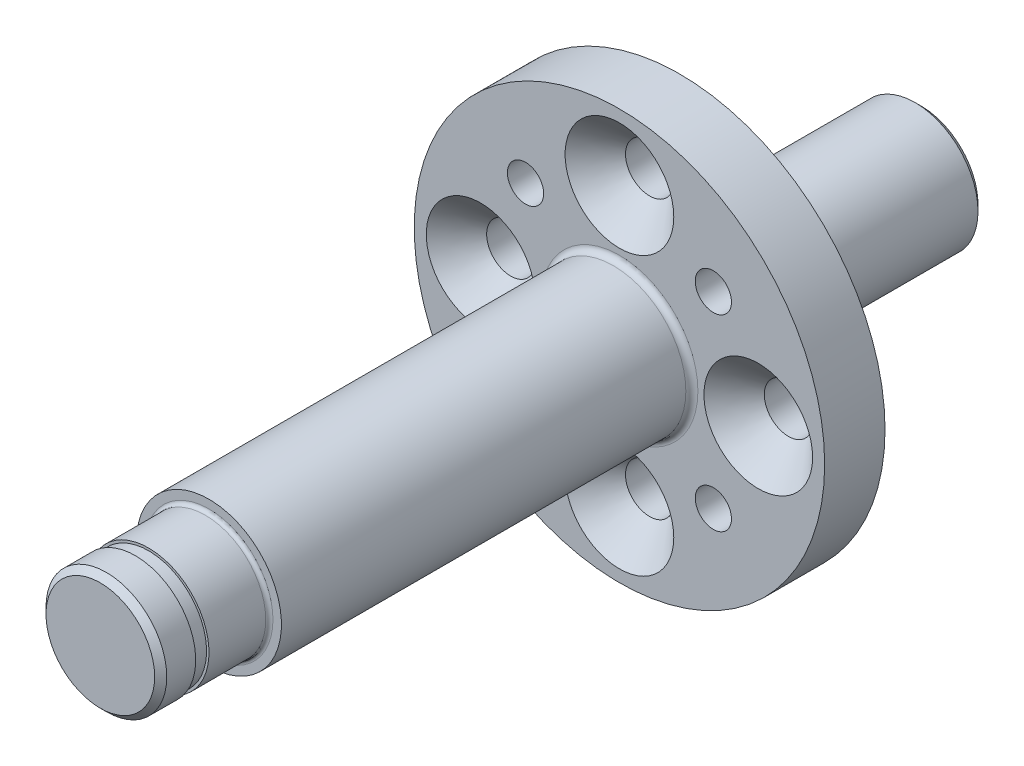
SolidWorks part; units mm, degrees
material "6063-T6"
ref_plane "Front Plane" through (0, 0, 0) normal (0, 0, 1) x (1, 0, 0)
ref_plane "Top Plane" through (0, 0, 0) normal (0, 1, 0) x (1, 0, 0)
ref_plane "Right Plane" through (0, 0, 0) normal (1, 0, 0) x (0, 0, -1)
sketch "Sketch1" plane through (0, 0, 0) normal (0, 0, 1) x (1, 0, 0)
  circle A0 centre (0, 0) radius 17
  dimension "D1" = 34
extrude "Boss-Extrude1" add sketch "Sketch1" along normal blind 5
sketch "Sketch3" plane through (0, 0, 0) normal (0, 0, -1) x (-1, 0, 0)
  circle A0 centre (0, 0) radius 5.2
  dimension "D1" = 10.4
extrude "Boss-Extrude3" add sketch "Sketch3" along normal blind 20
hole_wizard "CSK for M4 Hex Socket Countersunk Cap Screw1" positions "Sketch4" profile "Sketch5" countersink size "M4" standard "ISO" end condition through all
sketch "Sketch4" plane through (0, 0, 5) normal (0, 0, 1) x (1, 0, 0)
  circle A0 centre (0, 0) radius 11.5 construction
  circle A1 centre (0, 0) radius 17 construction
  point P0 (0, 11.5)
  point P7 (11.5, 0)
  point P9 (0, -11.5)
  point P11 (-11.5, 0)
  dimension "D1" = 23
sketch "Sketch5" plane through (0, 11.5, 5) normal (1, 0, 0) x (0, -1, 0)
  line L0 (0, 0) -> (0, 25)
  line L1 (0, 25) -> (2, 25)
  line L2 (2, 25) -> (2, 2.5)
  line L3 (2, 2.5) -> (4.5, 0)
  line L5 (4.5, 0) -> (0, 0)
  line L6 (-2, 2.5) -> (-4.5, 0) construction
  line L11 (0, -6.35) -> (0, 107.95) construction
  dimension "Thru Hole Dia." = 4
  dimension "Thru Hole Depth" = 25
  dimension "Near C'Sink Dia." = 9
  dimension "Near C'Sink Angle" = 90
hole_wizard "M4 Tapped Hole1" positions "Sketch6" profile "Sketch8" tap size "M4" standard "ISO" end condition through all
sketch "Sketch6" plane through (0, 0, 5) normal (0, 0, 1) x (1, 0, 0)
  line L0 (-11, 0) -> (11, 0) construction
  line L2 (-7.7782, -7.7782) -> (7.7782, 7.7782) construction
  line L3 (-7.7782, 7.7782) -> (7.7782, -7.7782) construction
  circle A0 centre (0, 0) radius 11 construction
  point P0 (7.7782, 7.7782)
  point P11 (-7.7782, -7.7782)
  point P16 (-7.7782, 7.7782)
  point P17 (7.7782, -7.7782)
  dimension "D1" = 22
  dimension "D2" = 45
cosmetic thread "Hole Thread1" parameters "D2"=4
cosmetic thread "Hole Thread2" parameters "D2"=4
cosmetic thread "Hole Thread3" parameters "D2"=4
cosmetic thread "Hole Thread4" parameters "D2"=4
sketch "Sketch8" plane through (7.7782, 7.7782, 5) normal (1, 0, 0) x (0, -1, 0)
  line L0 (0, 0) -> (0, 25)
  line L1 (0, 25) -> (1.5, 25)
  line L2 (1.5, 25) -> (1.5, 0)
  line L5 (1.5, 0) -> (0, 0)
  line L11 (0, -6.35) -> (0, 107.95) construction
  dimension "Thru Tap Drill Dia." = 3
  dimension "Thru Tap Drill Depth" = 25
ref_axis "Axis1" through (0, 0, -20) along (0, 0, 1)
sketch "Sketch9" plane through (0, 0, 0) normal (1, 0, 0) x (0, 0, -1)
  line L0 (-5, 6) -> (-39, 6)
  line L1 (-5, 17) -> (-5, -17) construction
  line L2 (-39, 6) -> (-39, 5)
  line L3 (-39, 5) -> (-44, 5)
  line L4 (-44, 5) -> (-44, 4.8)
  line L5 (-44, 4.8) -> (-45.1, 4.8)
  line L6 (-45.1, 4.8) -> (-45.1, 5)
  line L7 (-45.1, 5) -> (-48, 5)
  line L8 (-48, 5) -> (-48, 0)
  line L9 (20, 0) -> (-117.0078, 0) construction
  line L10 (-48, 0) -> (-5, 0)
  line L11 (-5, 0) -> (-5, 6)
  dimension "D1" = 5
  dimension "D2" = 1.1
  dimension "D3" = 2.9
  dimension "D4" = 6
  dimension "D5" = 5
  dimension "D6" = 4.8
  dimension "D7" = 34
revolve "Revolve1" add sketch "Sketch9" angle 360 about axis through (0, 0, -20) along (0, 0, 1)
chamfer "Chamfer1" distance 0.5 angle 45 2 edges at (-5, 0, 48) (-5.2, 0, -20)
fillet "Fillet1" radius 0.3 1 edges at (-5, 0, 39)
fillet "Fillet2" radius 0.5 2 edges at (-5.2, 0, 0) (-6, 0, 5)
